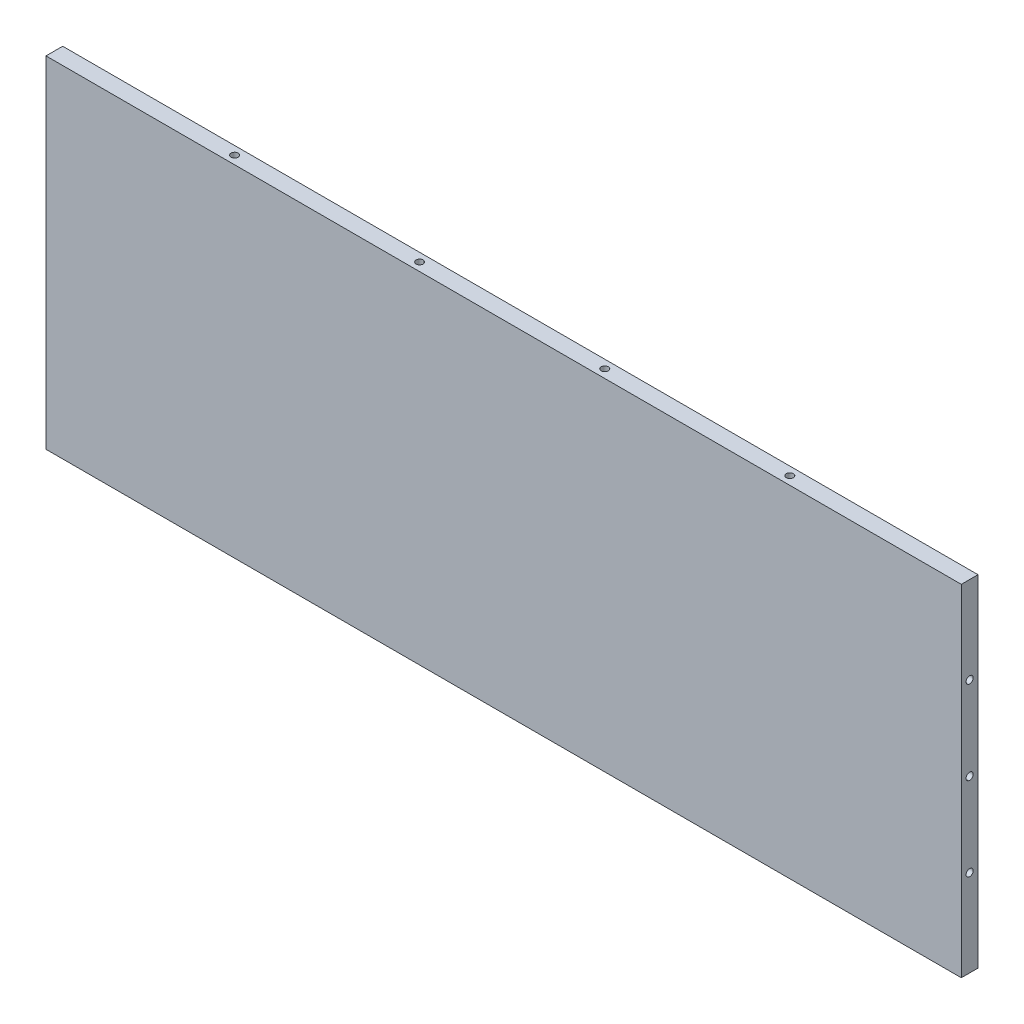
SolidWorks part; units mm, degrees
material "6061 Alloy"
ref_plane "Front Plane" through (0, 0, 0) normal (0, 0, 1) x (1, 0, 0)
ref_plane "Top Plane" through (0, 0, 0) normal (0, 1, 0) x (1, 0, 0)
ref_plane "Right Plane" through (0, 0, 0) normal (1, 0, 0) x (0, 0, -1)
sketch "Sketch1" plane through (0, 0, 0) normal (0, 0, 1) x (1, 0, 0)
  line L1 (0, 0) -> (347.98, 0)
  line L2 (0, 0) -> (0, 129.54)
  line L3 (0, 129.54) -> (347.98, 129.54)
  line L4 (347.98, 0) -> (347.98, 129.54)
  dimension "D1" = 347.98
  dimension "D2" = 129.54
extrude "Boss-Extrude1" add sketch "Sketch1" along normal blind 6.35
hole_wizard "#34 (0.111) Diameter Hole4" positions "Sketch8" profile "Sketch9" hole size "#34" standard "ANSI Inch"
sketch "Sketch8" plane through (0, 13.3032, -243.1125) normal (-1, 0, 0) x (0, 0, 1)
  line L1 (243.1125, 51.4668) -> (249.4625, 51.4668)
  line L2 (243.1125, 116.2368) -> (243.1125, -13.3032) construction
  line L3 (249.4625, 116.2368) -> (249.4625, -13.3032) construction
  line L4 (246.2875, 116.2368) -> (246.2875, -13.3032) construction
  line L5 (249.4625, 116.2368) -> (243.1125, 116.2368) construction
  line L6 (249.4625, -13.3032) -> (243.1125, -13.3032) construction
  point P0 (-105.5025, 81.9468)
  point P3 (-105.5025, 56.5468)
  point P6 (-105.5025, 31.1468)
  point P9 (246.2875, 83.2168)
  point P12 (246.2875, 51.4668)
  point P15 (246.2875, 19.7168)
  dimension "D2" = 31.75
  dimension "D3" = 31.75
sketch "Sketch9" plane through (0, 95.25, -348.615) normal (0, 1, 0) x (0, 0, 1)
  line L0 (0, 0) -> (0, 18.4935)
  line L1 (0, 18.4935) -> (1.1874, 17.78)
  line L2 (1.1874, 17.78) -> (1.1874, 0)
  line L3 (1.1874, 0) -> (0, 0)
  line L4 (0, 18.4935) -> (-1.1875, 17.78) construction
  line L5 (0, -6.35) -> (0, 107.95) construction
  dimension "Hole Dia." = 2.3749
  dimension "Hole Depth" = 17.78
  dimension "Drill Angle" = 118
hole_wizard "Tap Drill for #6-32 Tap1" positions "Sketch10" profile "Sketch11" hole size "#6-32" standard "ANSI Inch"
sketch "Sketch10" plane through (-62.7725, 129.54, -82.6024) normal (0, 1, 0) x (0, 0, -1)
  line L0 (-85.7774, -62.7725) -> (-85.7774, -410.7525) construction
  line L1 (-88.9524, -62.7725) -> (-82.6024, -62.7725) construction
  line L2 (-88.9524, -410.7525) -> (-82.6024, -410.7525) construction
  line L3 (-82.6024, -236.7625) -> (-88.9524, -236.7625) construction
  line L4 (-82.6024, -410.7525) -> (-82.6024, -62.7725) construction
  line L5 (-88.9524, -410.7525) -> (-88.9524, -62.7725) construction
  point P48 (-85.7774, -342.3757)
  point P51 (-85.7774, -272.0177)
  point P54 (-85.7774, -201.6597)
  point P57 (-85.7774, -131.3017)
  dimension "D1" = 35.1028
  dimension "D2" = 35.2552
  dimension "D3" = 70.358
  dimension "D4" = 70.358
sketch "Sketch11" plane through (279.6032, 129.54, 3.175) normal (1, 0, 0) x (0, 0, 1)
  line L0 (0, 0) -> (0, 18.5927)
  line L1 (0, 18.5927) -> (1.3525, 17.78)
  line L2 (1.3525, 17.78) -> (1.3525, 0)
  line L3 (1.3525, 0) -> (0, 0)
  line L4 (0, 18.5927) -> (-1.3525, 17.78) construction
  line L5 (0, -6.35) -> (0, 107.95) construction
  dimension "Hole Dia." = 2.7051
  dimension "Hole Depth" = 17.78
  dimension "Drill Angle" = 118
hole_wizard "Tap Drill for #6-32 Tap2" positions "Sketch12" profile "Sketch13" hole size "#6-32" standard "ANSI Inch"
sketch "Sketch12" plane through (-62.7725, 0, -82.6024) normal (0, -1, 0) x (0, 0, 1)
  line L0 (85.7774, -62.7725) -> (85.7774, -410.7525) construction
  line L1 (88.9524, -62.7725) -> (82.6024, -62.7725) construction
  line L2 (88.9524, -410.7525) -> (82.6024, -410.7525) construction
  line L3 (85.7774, -410.7525) -> (88.9524, -236.7625) construction
  line L4 (88.9524, -62.7725) -> (88.9524, -410.7525) construction
  line L5 (88.9524, -236.7625) -> (82.6024, -236.7625) construction
  line L6 (82.6024, -62.7725) -> (82.6024, -410.7525) construction
  point P48 (85.7774, -131.3017)
  point P51 (85.7774, -201.6597)
  point P54 (85.7774, -272.0177)
  point P57 (85.7774, -342.3757)
  dimension "D1" = 35.1028
  dimension "D2" = 35.2552
  dimension "D3" = 70.358
  dimension "D4" = 70.358
sketch "Sketch13" plane through (68.5292, 0, 3.175) normal (1, 0, 0) x (0, 0, -1)
  line L0 (0, 0) -> (0, 18.5927)
  line L1 (0, 18.5927) -> (1.3525, 17.78)
  line L2 (1.3525, 17.78) -> (1.3525, 0)
  line L3 (1.3525, 0) -> (0, 0)
  line L4 (0, 18.5927) -> (-1.3525, 17.78) construction
  line L5 (0, -6.35) -> (0, 107.95) construction
  dimension "Hole Dia." = 2.7051
  dimension "Hole Depth" = 17.78
  dimension "Drill Angle" = 118
hole_wizard "Tap Drill for #6-32 Tap3" positions "Sketch15" profile "Sketch14" hole size "#6-32" standard "ANSI Inch"
sketch "Sketch15" plane through (347.98, 0, 0) normal (1, 0, 0) x (0, 0, -1)
  line L0 (-3.175, 129.54) -> (-3.175, 0) construction
  line L1 (-6.35, 129.54) -> (0, 129.54) construction
  line L2 (-6.35, 0) -> (0, 0) construction
  line L3 (-3.175, 0) -> (-6.35, 64.77) construction
  line L4 (-6.35, 0) -> (-6.35, 129.54) construction
  line L5 (-6.35, 64.77) -> (0, 64.77) construction
  line L6 (0, 0) -> (0, 129.54) construction
  point P17 (-3.175, 64.77)
  point P19 (-3.175, 96.52)
  point P21 (-3.175, 33.02)
  dimension "D1" = 31.75
  dimension "D2" = 31.75
sketch "Sketch14" plane through (347.98, 64.77, 3.175) normal (0, 1, 0) x (0, 0, -1)
  line L0 (0, 0) -> (0, 18.5927)
  line L1 (0, 18.5927) -> (1.3525, 17.78)
  line L2 (1.3525, 17.78) -> (1.3525, 0)
  line L5 (1.3525, 0) -> (0, 0)
  line L10 (0, 18.5927) -> (-1.3526, 17.78) construction
  line L11 (0, -6.35) -> (0, 107.95) construction
  dimension "Hole Dia." = 2.7051
  dimension "Hole Depth" = 17.78
  dimension "Drill Angle" = 118
